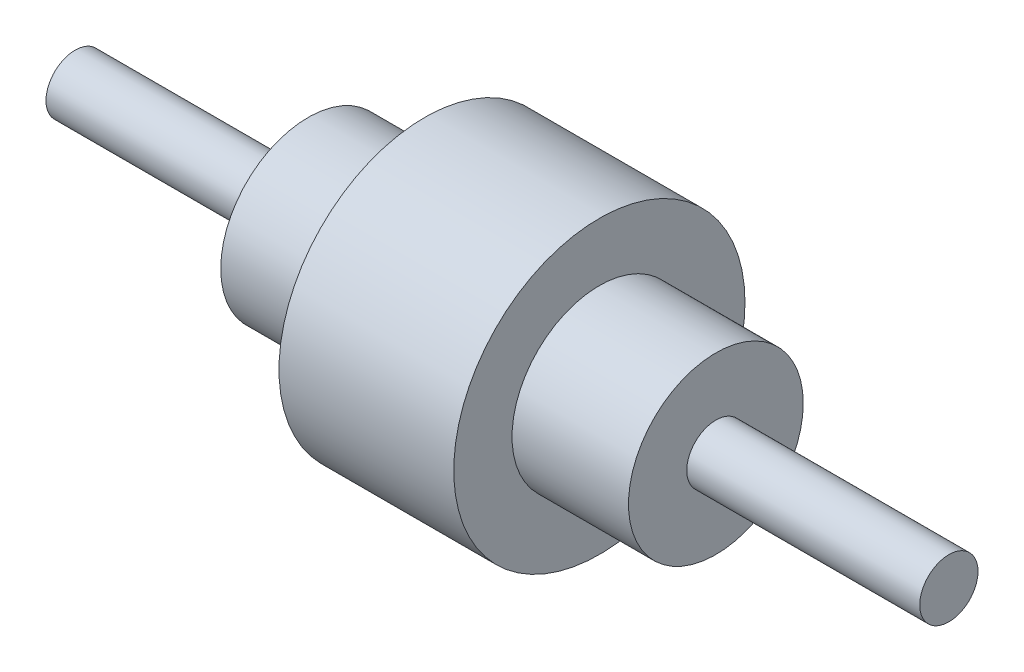
SolidWorks part; units mm, degrees
ref_plane "Front Plane" through (0, 0, 0) normal (0, 0, 1) x (1, 0, 0)
ref_plane "Top Plane" through (0, 0, 0) normal (0, 1, 0) x (1, 0, 0)
ref_plane "Right Plane" through (0, 0, 0) normal (1, 0, 0) x (0, 0, -1)
sketch "Sketch1" plane through (0, 0, 0) normal (1, 0, 0) x (0, 0, -1)
  circle A0 centre (0, 0) radius 50
extrude "Boss-Extrude1" add sketch "Sketch1" along normal blind 30
sketch "Sketch2" plane through (30, 0, 0) normal (1, 0, 0) x (0, 0, -1)
  circle A0 centre (0, 0) radius 30
extrude "Boss-Extrude2" add sketch "Sketch2" along normal blind 30
sketch "Sketch3" plane through (60, 0, 0) normal (1, 0, 0) x (0, 0, -1)
  circle A0 centre (0, 0) radius 10
extrude "Boss-Extrude3" add sketch "Sketch3" along normal blind 80
mirror "Mirror1" about plane through (0, 0, 0) normal (1, 0, 0) of "Boss-Extrude1", "Boss-Extrude2", "Boss-Extrude3"
sketch "Sketch7" plane through (-60, 0, 0) normal (-1, 0, 0) x (0, 0, 1)
  circle A0 centre (0, 0) radius 30
extrude "Boss-Extrude4" add sketch "Sketch7" along normal blind 10
sketch "Sketch8" plane through (-140, 0, 0) normal (-1, 0, 0) x (0, 0, 1)
  circle A0 centre (0, 0) radius 10
extrude "Boss-Extrude5" add sketch "Sketch8" along normal blind 10
sketch "Sketch9" plane through (60, 0, 0) normal (1, 0, 0) x (0, 0, -1)
  circle A0 centre (0, 0) radius 30
extrude "Boss-Extrude6" add sketch "Sketch9" along normal blind 10
sketch "Sketch10" plane through (140, 0, 0) normal (1, 0, 0) x (0, 0, -1)
  circle A0 centre (0, 0) radius 10
extrude "Boss-Extrude7" add sketch "Sketch10" along normal blind 10
